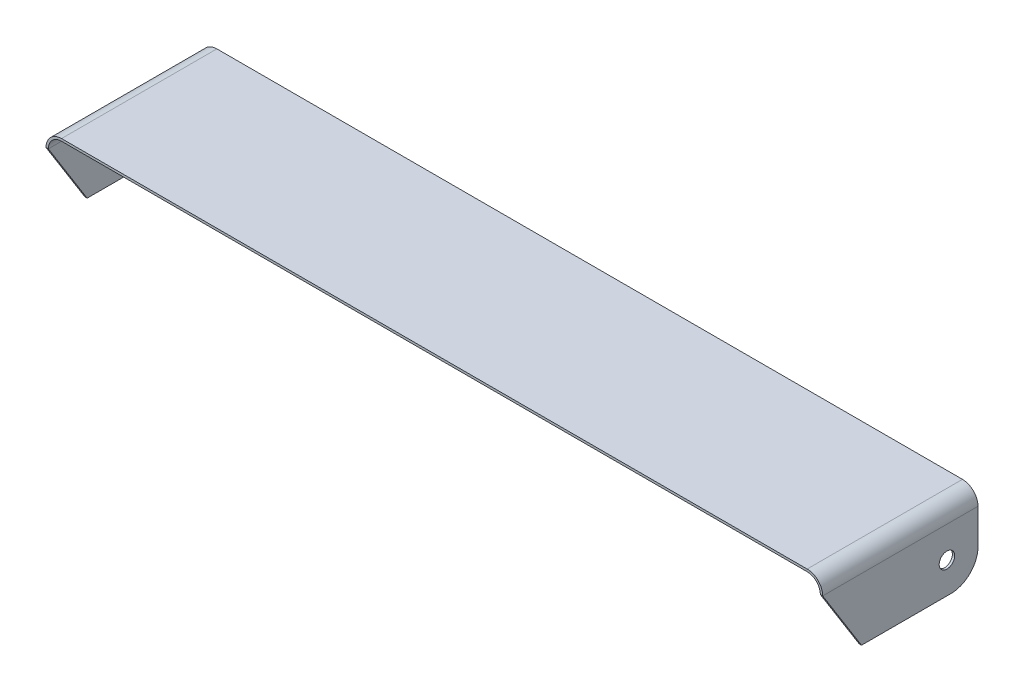
SolidWorks part; units mm, degrees
ref_plane "Front Plane" through (0, 0, 0) normal (0, 0, 1) x (1, 0, 0)
ref_plane "Top Plane" through (0, 0, 0) normal (0, 1, 0) x (1, 0, 0)
ref_plane "Right Plane" through (0, 0, 0) normal (1, 0, 0) x (0, 0, -1)
sketch "Sketch1" plane through (0, 0, 0) normal (0, 0, 1) x (1, 0, 0)
  line L0 (-500, 0) -> (-500, 80)
  line L1 (-480, 100) -> (480, 100)
  line L2 (500, 80) -> (500, 0)
  line L3 (-497, 0) -> (-497, 80)
  line L4 (-480, 97) -> (480, 97)
  line L5 (497, 80) -> (497, 0)
  line L6 (-500, 0) -> (-497, 0)
  line L7 (497, 0) -> (500, 0)
  arc A0 (500, 80) -> (480, 100) centre (480, 80) ccw
  arc A1 (-480, 100) -> (-500, 80) centre (-480, 80) ccw
  arc A2 (-480, 97) -> (-497, 80) centre (-480, 80) ccw
  arc A3 (497, 80) -> (480, 97) centre (480, 80) ccw
  point P8 (500, 100)
  point P11 (-500, 100)
  dimension "D4" = 20
  dimension "D1" = 1000
  dimension "D2" = 100
  dimension "D3" = 500
  dimension "D5" = 3
extrude "Boss-Extrude1" add sketch "Sketch1" along normal mid plane 200
sketch "Sketch2" plane through (500, 0, 0) normal (1, 0, 0) x (0, 0, -1)
  line L0 (-100, 80) -> (-100, 0)
  line L1 (-100, 0) -> (-100, 80) construction
  line L2 (-100, 0) -> (-50, 0)
  line L3 (-100, 0) -> (100, 0) construction
  line L4 (-50, 0) -> (-100, 80)
  dimension "D1" = 50
  dimension "D2" = 80
extrude "Cut-Extrude1" cut sketch "Sketch2" against normal through all
sketch "Sketch3" plane through (500, 0, 0) normal (1, 0, 0) x (0, 0, -1)
  line L0 (100, 0) -> (100, 80) construction
  line L1 (-100, 100) -> (100, 100) construction
  circle A0 centre (60, 40) radius 10
  dimension "D3" = 20
  dimension "D1" = 40
  dimension "D2" = 60
extrude "Cut-Extrude2" cut sketch "Sketch3" against normal through all
fillet "Fillet1" radius 35 2 edges at (-498.5, 0, -100) (498.5, 0, -100)
